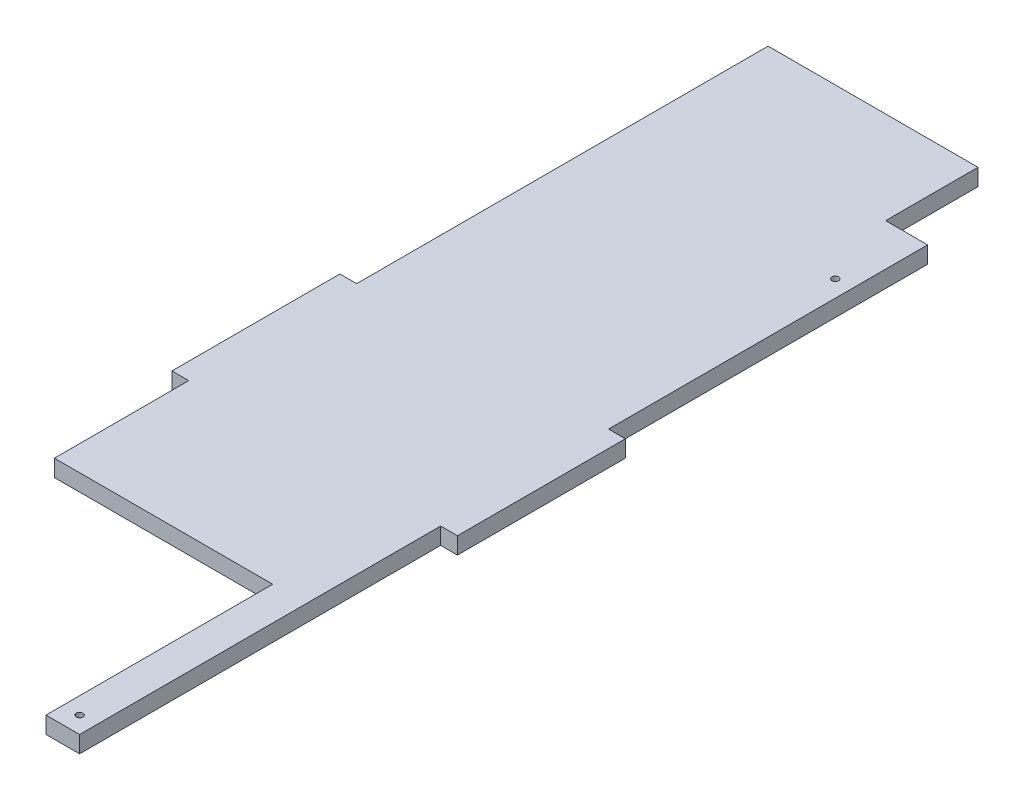
SolidWorks part; units mm, degrees
ref_plane "Front Plane" through (0, 0, 0) normal (0, 0, 1) x (1, 0, 0)
ref_plane "Top Plane" through (0, 0, 0) normal (0, 1, 0) x (1, 0, 0)
ref_plane "Right Plane" through (0, 0, 0) normal (1, 0, 0) x (0, 0, -1)
sketch "Sketch1" plane through (0, 0, 0) normal (0, 1, 0) x (1, 0, 0)
  line L0 (-75, 215) -> (-75, 135)
  line L1 (75, 215) -> (75, 0)
  line L2 (-75, 560) -> (75, 560)
  line L3 (-75, 215) -> (-85, 215)
  line L4 (-85, 215) -> (-85, 315)
  line L5 (-85, 315) -> (-75, 315)
  line L6 (-75, 315) -> (-75, 560)
  line L7 (75, 0) -> (55, 0)
  line L8 (75, 215) -> (85, 215)
  line L9 (85, 215) -> (85, 315)
  line L10 (85, 315) -> (75, 315)
  line L11 (75, 315) -> (75, 560)
  line L12 (55, 0) -> (55, 135)
  line L13 (55, 135) -> (-75, 135)
extrude "Boss-Extrude1" add sketch "Sketch1" along normal blind 10
sketch "Sketch2" plane through (0, 10, 0) normal (0, 1, 0) x (1, 0, 0)
  line L1 (75, 560) -> (50, 560)
  line L2 (75, 560) -> (75, 505)
  line L3 (75, 505) -> (50, 505)
  line L4 (50, 560) -> (50, 505)
  circle A0 centre (65, 10) radius 2
  circle A1 centre (65, 460) radius 2
extrude "Cut-Extrude1" cut sketch "Sketch2" against normal blind 10
